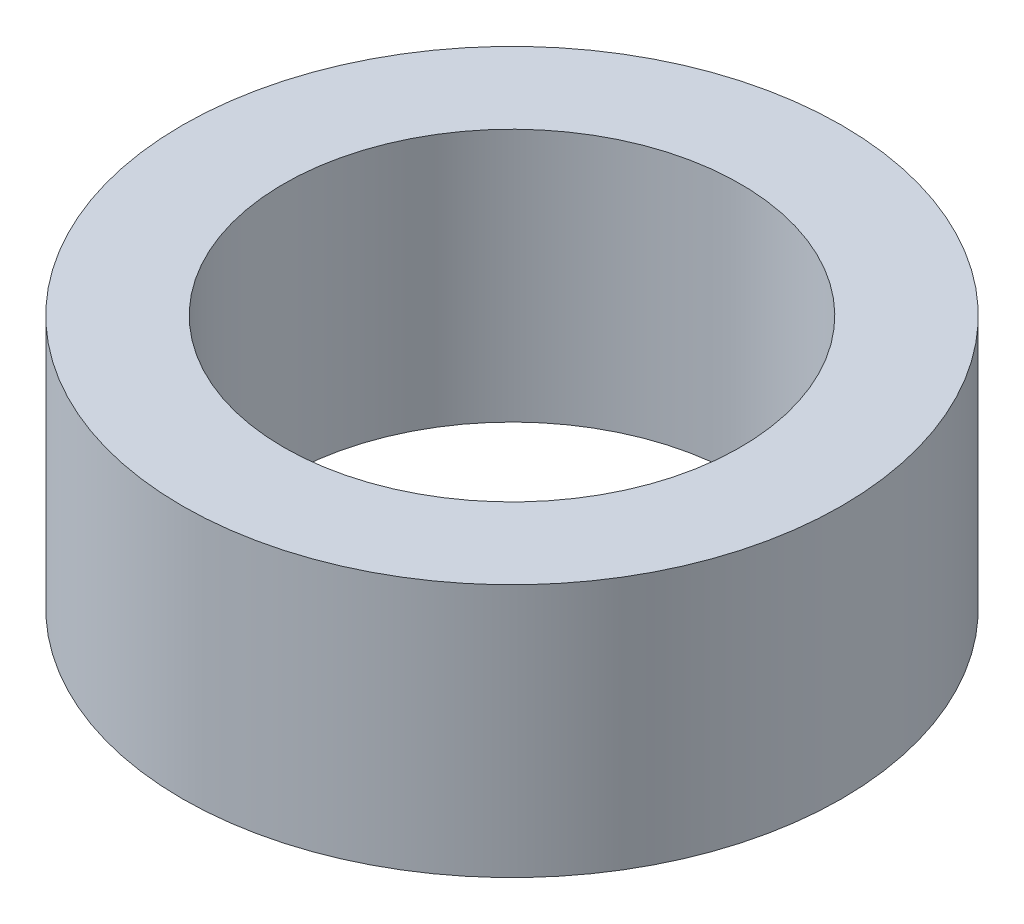
SolidWorks part; units mm, degrees
ref_plane "Front Plane" through (0, 0, 0) normal (0, 0, 1) x (1, 0, 0)
ref_plane "Top Plane" through (0, 0, 0) normal (0, 1, 0) x (1, 0, 0)
ref_plane "Right Plane" through (0, 0, 0) normal (1, 0, 0) x (0, 0, -1)
sketch "Sketch1" plane through (0, 0, 0) normal (0, 1, 0) x (1, 0, 0)
  circle A0 centre (0, 0) radius 1.8
  circle A1 centre (0, 0) radius 2.6
  dimension "D1" = 3.6
  dimension "D2" = 5.2
extrude "Boss-Extrude1" add sketch "Sketch1" along normal blind 2
